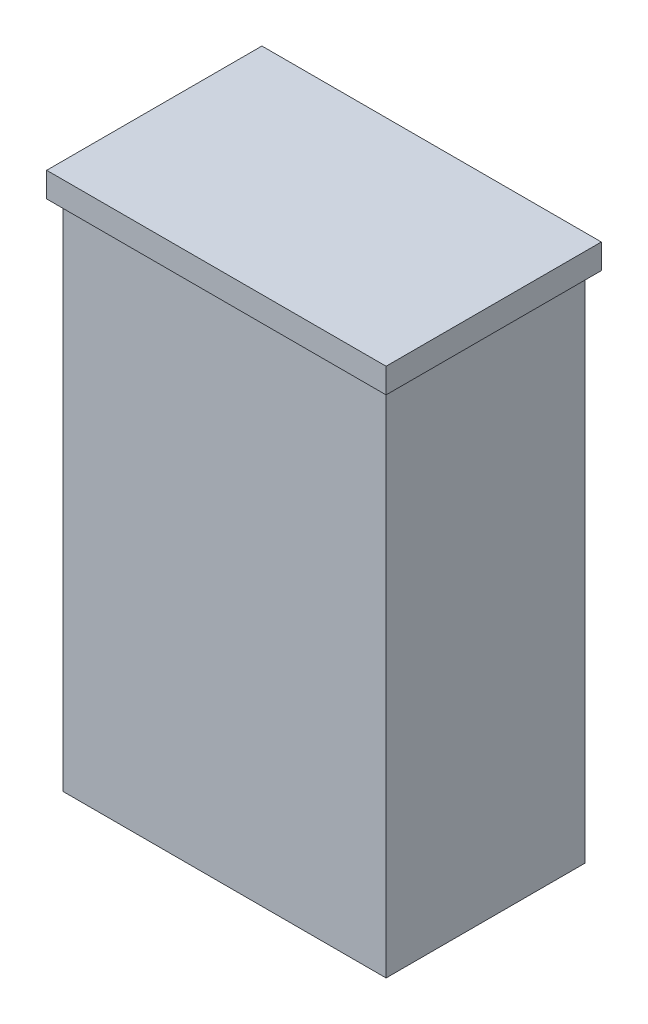
SolidWorks part; units mm, degrees
ref_plane "Piano frontale" through (0, 0, 0) normal (0, 0, 1) x (1, 0, 0)
ref_plane "Piano superiore" through (0, 0, 0) normal (0, 1, 0) x (1, 0, 0)
ref_plane "Piano destro" through (0, 0, 0) normal (1, 0, 0) x (0, 0, -1)
sketch "Schizzo1" plane through (0, 0, 0) normal (0, 1, 0) x (1, 0, 0)
  line L1 (-19.5, 12) -> (19.5, 12)
  line L2 (-19.5, 12) -> (-19.5, -12)
  line L3 (-19.5, -12) -> (19.5, -12)
  line L4 (19.5, 12) -> (19.5, -12)
  point P4 (0, 12)
  point P6 (19.5, 0)
  dimension "D1" = 39
  dimension "D2" = 24
extrude "Estrusione-Estrusione1" add sketch "Schizzo1" along normal blind 62
sketch "Schizzo2" plane through (0, 62, 0) normal (0, 1, 0) x (1, 0, 0)
  line L7 (-20.5, 13) -> (-20.5, -13)
  line L8 (-20.5, -13) -> (20.5, -13)
  line L9 (20.5, -13) -> (20.5, 13)
  line L10 (20.5, 13) -> (-20.5, 13)
  line L11 (-19.5, 12) -> (-19.5, -12)
  line L12 (-19.5, -12) -> (19.5, -12)
  line L13 (19.5, -12) -> (19.5, 12)
  line L14 (19.5, 12) -> (-19.5, 12)
  line L15 (-19.5, 12) -> (-19.5, -12) construction
  line L16 (-19.5, -12) -> (19.5, -12) construction
  line L17 (19.5, -12) -> (19.5, 12) construction
  line L18 (19.5, 12) -> (-19.5, 12) construction
  dimension "D1" = 0
  dimension "D2" = 1
extrude "Estrusione-Estrusione2" add sketch "Schizzo2" along normal blind 3
